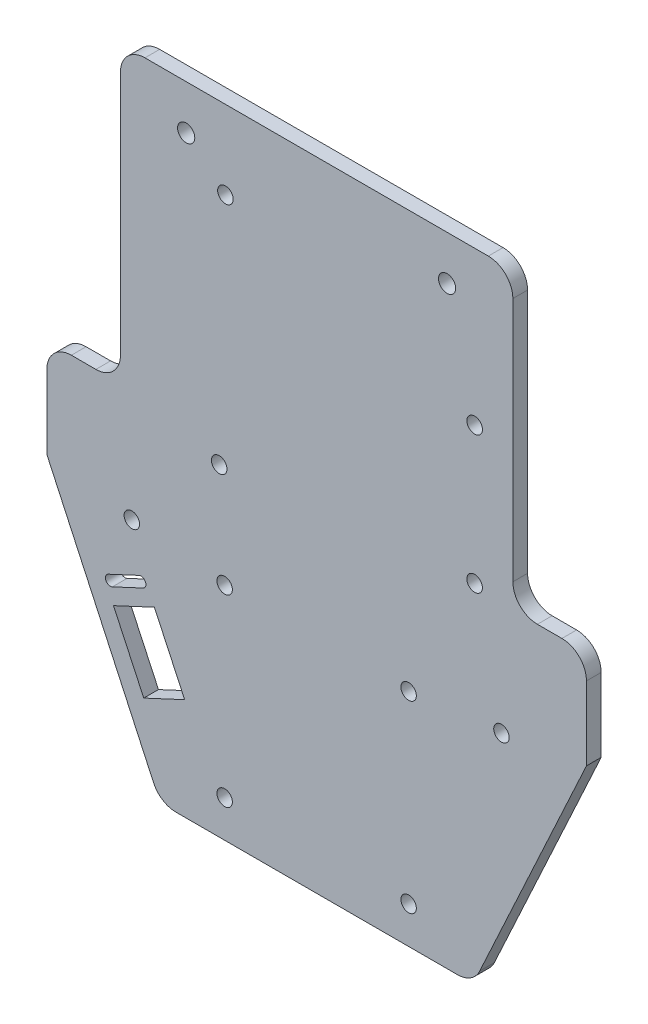
SolidWorks part; units mm, degrees
ref_plane "Front Plane" through (0, 0, 0) normal (0, 0, 1) x (1, 0, 0)
ref_plane "Top Plane" through (0, 0, 0) normal (0, 1, 0) x (1, 0, 0)
ref_plane "Right Plane" through (0, 0, 0) normal (1, 0, 0) x (0, 0, -1)
sketch "Sketch1" plane through (0, 0, 0) normal (0, 0, 1) x (1, 0, 0)
  line L0 (0, 76.2257) -> (0, -152.1284) construction
  line L1 (50, 76.2257) -> (-50, 76.2257) construction
  line L3 (-55, -3.7743) -> (-33.2358, -50.8801)
  line L5 (-55, 16.2257) -> (55, 16.2257) construction
  line L6 (-40, 16.2257) -> (-40, 76.2257) construction
  line L7 (-55, 16.2257) -> (-40, 16.2257)
  line L8 (-40, 16.2257) -> (-40, 76.2257)
  line L9 (55, 16.2257) -> (40, 16.2257)
  line L10 (40, 16.2257) -> (40, 76.2257)
  line L11 (-35.4769, -15.5049) -> (-28.5793, -15.5049) construction
  line L12 (-41.4115, -23.6907) -> (-33.0735, -19.8026)
  line L13 (-41.4115, -23.6907) -> (-35.2413, -36.9228)
  line L14 (-35.2413, -36.9228) -> (-26.9032, -33.0347)
  line L15 (-33.0735, -19.8026) -> (-26.9032, -33.0347)
  line L16 (-41.636, -20.4853) -> (-35.3847, -17.5702)
  line L17 (-42.4812, -18.6727) -> (-36.2299, -15.7576)
  line L30 (-71.8609, -108.9557) -> (-9.4029, -131.5658)
  line L34 (9.4029, -131.5658) -> (71.8609, -108.9557)
  line L35 (77.535, -103.7471) -> (82.1483, -93.7622)
  line L36 (80.6854, -83.0863) -> (73.0383, -74.1022)
  line L37 (73.0383, -74.1022) -> (67.9785, -85.0536)
  line L38 (63.4395, -87.9565) -> (25.3479, -87.9565)
  line L39 (20.3479, -82.9565) -> (20.3479, -78.7743)
  line L40 (20.3479, -78.7743) -> (55, -3.7743)
  line L41 (55, -3.7743) -> (55, 28.3474)
  line L46 (50, 76.2257) -> (-50, 76.2257)
  line L47 (-55, 71.2257) -> (-55, 43.3474)
  line L52 (-55, -3.7743) -> (-20.3479, -78.7743)
  line L53 (-20.3479, -78.7743) -> (-20.3479, -82.9565)
  line L54 (-25.3479, -87.9565) -> (-63.4395, -87.9565)
  line L55 (-67.9785, -85.0536) -> (-73.0383, -74.1022)
  line L56 (-73.0383, -74.1022) -> (-80.6854, -83.0863)
  line L57 (-82.1483, -93.7622) -> (-77.535, -103.7471)
  line L69 (55, -3.7743) -> (55, 16.2257)
  line L74 (40, 76.2257) -> (-40, 76.2257)
  line L105 (-9.4029, -131.5658) -> (9.4029, -131.5658)
  line L106 (-9.4029, -131.5658) -> (9.4029, -131.5658)
  line L195 (55, 43.3474) -> (55, 71.2257)
  line L197 (-55, 28.3474) -> (-55, -3.7743)
  line L198 (-55, 16.2257) -> (-55, -3.7743)
  line L199 (-51.8, 28.3474) -> (-55, 28.3474)
  line L200 (-51.8, 28.3474) -> (-55, 28.3474)
  line L201 (55, 28.3474) -> (51.8, 28.3474)
  line L203 (51.8, 28.3474) -> (51.8, 43.3474)
  line L205 (51.8, 43.3474) -> (55, 43.3474)
  line L207 (-55, 43.3474) -> (-51.8, 43.3474)
  line L209 (-51.8, 43.3474) -> (-51.8, 28.3474)
  line L789 (-28.6969, -53.783) -> (28.6969, -53.783)
  line L790 (55, -3.7743) -> (33.2358, -50.8801)
  circle A0 centre (-37.674, -6.6651) radius 1.575
  circle A2 centre (37.674, -6.6651) radius 1.575
  circle A4 centre (32.2084, 17.0569) radius 1.5875
  circle A5 centre (32.2084, 44.9969) radius 1.5875
  circle A6 centre (-19.8616, 11.9769) radius 1.5875
  circle A7 centre (-18.5916, 60.2369) radius 1.5875
  arc A10 (71.8609, -108.9557) -> (77.535, -103.7471) centre (68.4571, -99.5529) ccw
  arc A11 (82.1483, -93.7622) -> (80.6854, -83.0863) centre (73.0704, -89.568) ccw
  arc A12 (63.4395, -87.9565) -> (67.9785, -85.0536) centre (63.4395, -82.9565) ccw
  arc A13 (20.3479, -82.9565) -> (25.3479, -87.9565) centre (25.3479, -82.9565) ccw
  arc A14 (55, 71.2257) -> (50, 76.2257) centre (50, 71.2257) ccw
  arc A15 (-50, 76.2257) -> (-55, 71.2257) centre (-50, 71.2257) ccw
  arc A16 (-25.3479, -87.9565) -> (-20.3479, -82.9565) centre (-25.3479, -82.9565) ccw
  arc A17 (-67.9785, -85.0536) -> (-63.4395, -87.9565) centre (-63.4395, -82.9565) ccw
  arc A18 (-80.6854, -83.0863) -> (-82.1483, -93.7622) centre (-73.0704, -89.568) ccw
  arc A19 (-77.535, -103.7471) -> (-71.8609, -108.9557) centre (-68.4571, -99.5529) ccw
  circle A30 centre (-26.592, 67.1804) radius 1.75
  circle A31 centre (26.592, 67.1804) radius 1.75
  arc A32 (-41.636, -20.4853) -> (-42.4812, -18.6727) centre (-42.0586, -19.579) cw
  arc A33 (-35.3847, -17.5702) -> (-36.2299, -15.7576) centre (-35.8073, -16.6639) ccw
  arc A290 (28.6969, -53.783) -> (33.2358, -50.8801) centre (28.6969, -48.783) ccw
  arc A291 (-28.6969, -53.783) -> (-33.2358, -50.8801) centre (-28.6969, -48.783) cw
  circle A312 centre (-18.75, -8.7496) radius 1.575
  circle A313 centre (18.75, -8.7496) radius 1.575
  circle A314 centre (-18.75, -46.2496) radius 1.575
  circle A315 centre (18.75, -46.2496) radius 1.575
  point P42 (0, 16.2257)
  point P84 (-32.0281, -15.5049)
  dimension "D2" = 3.15
  dimension "D3" = 20
  dimension "D4" = 5
  dimension "D6" = 3.15
  dimension "D7" = 3.15
  dimension "D8" = 3.15
  dimension "D9" = 3.15
  dimension "D5" = 15
  dimension "D10" = 9.2
  dimension "D11" = 14.6
  dimension "D14" = 3
  dimension "D1" = 0
extrude "Boss-Extrude1" add sketch "Sketch1" along normal blind 3
fillet "Fillet1" radius 5 6 edges at (40, 76.2257, 1.5) (40, 16.2257, 1.5) (-40, 76.2257, 1.5) (-40, 16.2257, 1.5) (-55, 16.2257, 1.5) (55, 16.2257, 1.5)
